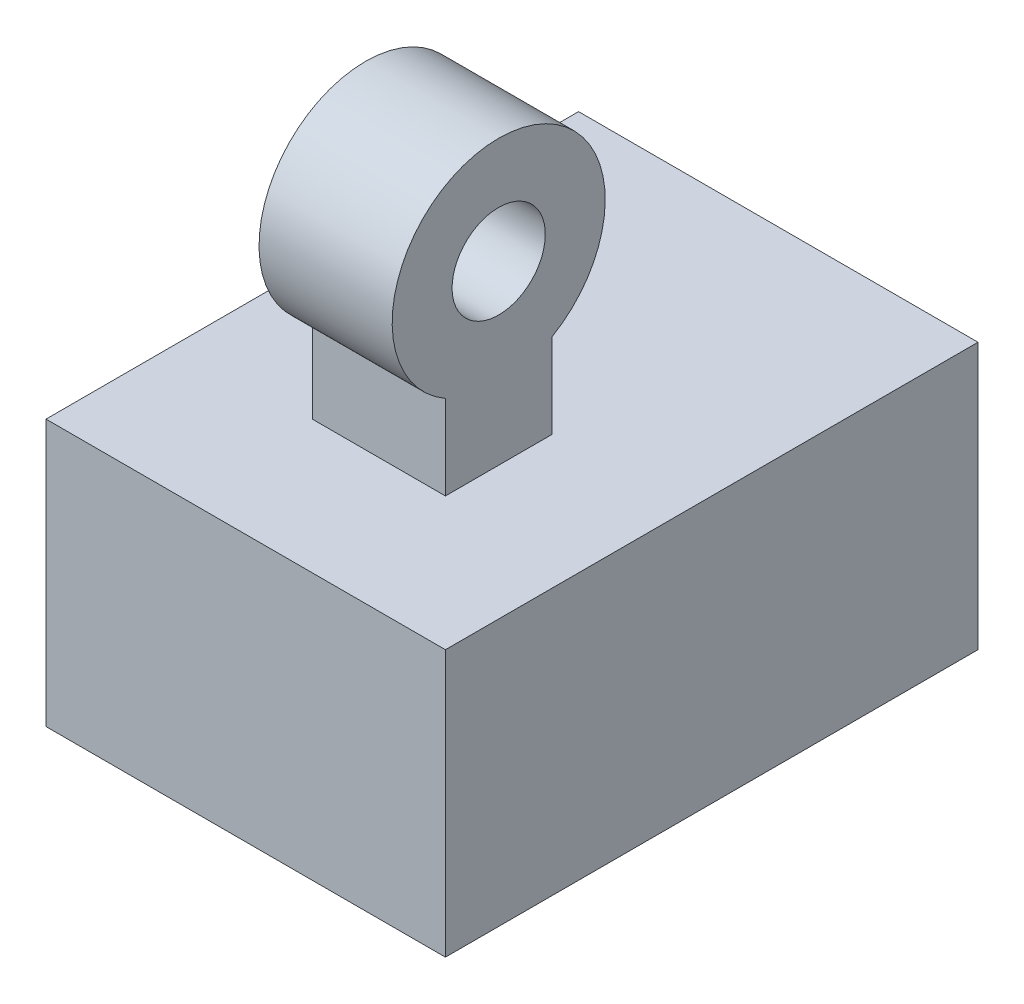
SolidWorks part; units mm, degrees
ref_plane "Plan de face" through (0, 0, 0) normal (0, 0, 1) x (1, 0, 0)
ref_plane "Plan de dessus" through (0, 0, 0) normal (0, 1, 0) x (1, 0, 0)
ref_plane "Plan de droite" through (0, 0, 0) normal (1, 0, 0) x (0, 0, -1)
sketch "Esquisse1" plane through (0, 0, 0) normal (0, 0, 1) x (1, 0, 0)
  line L1 (-71.9564, 20.6735) -> (-41.9564, 20.6735)
  line L2 (-71.9564, 20.6735) -> (-71.9564, 0.6735)
  line L3 (-71.9564, 0.6735) -> (-41.9564, 0.6735)
  line L4 (-41.9564, 20.6735) -> (-41.9564, 0.6735)
  dimension "D1" = 30
  dimension "D2" = 20
  dimension "D3" = 30
extrude "Boss.-Extru.1" add sketch "Esquisse1" along normal blind 40
sketch "Esquisse2" plane through (0, 0, 40) normal (0, 0, 1) x (1, 0, 0)
sketch "Esquisse3" plane through (0, 20.6735, 0) normal (0, 1, 0) x (1, 0, 0)
  line L0 (-71.9564, -40) -> (-71.9564, 0) construction
  line L1 (-61.9564, -30) -> (-51.9564, -30)
  line L2 (-61.9564, -30) -> (-61.9564, -22)
  line L3 (-61.9564, -22) -> (-51.9564, -22)
  line L4 (-51.9564, -30) -> (-51.9564, -22)
  line L5 (-41.9564, -40) -> (-41.9564, 0) construction
  line L6 (-41.9564, -40) -> (-71.9564, -40) construction
  dimension "D1" = 10
  dimension "D2" = 10
  dimension "D3" = 10
  dimension "D4" = 8
extrude "Boss.-Extru.2" add sketch "Esquisse3" along normal blind 8
sketch "Esquisse4" plane through (-41.9564, 0, 0) normal (1, 0, 0) x (0, 0, -1)
  line L0 (-30, 28.6735) -> (-30, 20.6735) construction
  line L1 (-22, 28.6735) -> (-22, 20.6735) construction
  line L2 (-26, 33.3861) -> (-24.2313, -24.1492) construction
  line L3 (14.598, 23.7163) -> (16.9652, -18.7209) construction
  arc A0 (-26.3, 39.6224) -> (-19.8004, 32.6478) centre (-26, 33.3861) ccw
  arc A1 (14.3203, 29.9526) -> (20.7966, 22.9781) centre (14.598, 23.7163) ccw
  dimension "D1" = 3.7
  dimension "D2" = 4
sketch "Esquisse5" plane through (0, 0, 40) normal (0, 0, 1) x (1, 0, 0)
  line L0 (-68.8876, 47.2139) -> (-105.2482, 45.1998) construction
sketch "Esquisse6" plane through (-51.9564, 0, 0) normal (1, 0, 0) x (0, 0, -1)
  line L0 (-26, 37.0793) -> (-26, -6.5925) construction
  line L2 (-30, 28.6735) -> (-22, 28.6735) construction
  circle A0 centre (-26, 33.9446) radius 8
  circle A1 centre (-26, 33.9446) radius 3.5
  dimension "D3" = 16
  dimension "D4" = 7
  dimension "D1" = 4
  dimension "D2" = 90
extrude "Boss.-Extru.3" add sketch "Esquisse6" against normal blind 10
